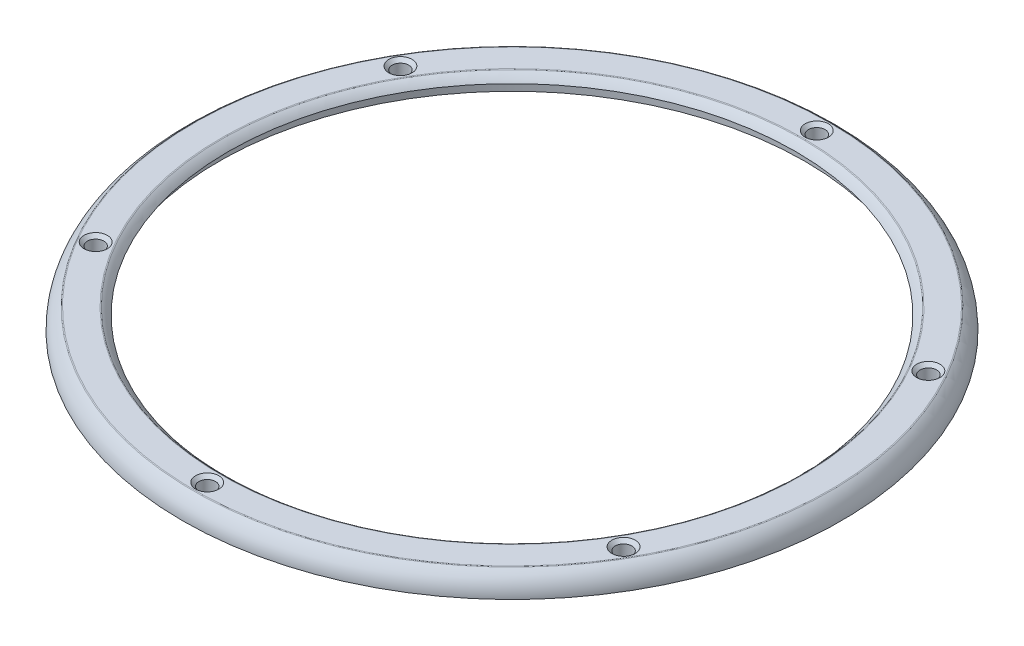
SolidWorks part; units mm, degrees
ref_plane "Plan de face" through (0, 0, 0) normal (0, 0, 1) x (1, 0, 0)
ref_plane "Plan de dessus" through (0, 0, 0) normal (0, 1, 0) x (1, 0, 0)
ref_plane "Plan de droite" through (0, 0, 0) normal (1, 0, 0) x (0, 0, -1)
sketch "Esquisse1" plane through (0, 0, 0) normal (1, 0, 0) x (0, 0, -1)
  line L0 (0, 0) -> (0, 12.2133) construction
  line L1 (-17.62, 0) -> (-19.82, 0)
  line L2 (-19.1492, 1.25) -> (-17.4908, 1.25)
  line L3 (-17.0511, 0.8) -> (-17.62, 0.8)
  line L4 (-17.62, 0.8) -> (-17.62, 0)
  arc A0 (-17.0511, 0.8) -> (-17.4908, 1.25) centre (-18.32, 0) ccw
  circle A1 centre (-18.32, 0) radius 1.5 construction
  arc A2 (-19.1492, 1.25) -> (-19.82, 0) centre (-18.32, 0) ccw
  dimension "D2" = 1.5
  dimension "D3" = 17.62
  dimension "D1" = 18.32
  dimension "D4" = 0.8
  dimension "D5" = 0.45
revolve "Révolution1" add sketch "Esquisse1" angle 360 about L0
sketch "Esquisse2" plane through (0, 0, 0) normal (0, 1, 0) x (1, 0, 0)
  circle A0 centre (0, 0) radius 18.32 construction
  dimension "D1" = 36.64
sketch "Esquisse4" plane through (0, 0, 0) normal (1, 0, 0) x (0, 0, -1)
  line L0 (0, -4.4077) -> (0, 4.6561) construction
sketch "Esquisse3" plane through (0, 0, 0) normal (0, 1, 0) x (1, 0, 0)
  line L0 (0, 18.33) -> (0, 0) construction
  circle A0 centre (0, 18.33) radius 0.5
  dimension "D1" = 1
  dimension "D2" = 18.33
extrude "Enlèv. mat.-Extru.1" cut sketch "Esquisse3" along normal through all
chamfer "Chanfrein1" distance 0.2 angle 45 1 edges at (0, 1.25, -17.83)
pattern_circular "Répétition circulaire1" count 6 over 360 about axis through (0, 0, 0) along (0, 1, 0) of "Enlèv. mat.-Extru.1", "Chanfrein1"
sketch "Esquisse5" plane through (0, 0, 0) normal (0, 1, 0) x (1, 0, 0)
  circle A0 centre (0, 18.33) radius 0.675 construction
  dimension "D1" = 1.35
fillet "Congé1" radius 0.1 2 edges at (0, 1.25, -19.1492) (0, 1.25, -17.4908)
